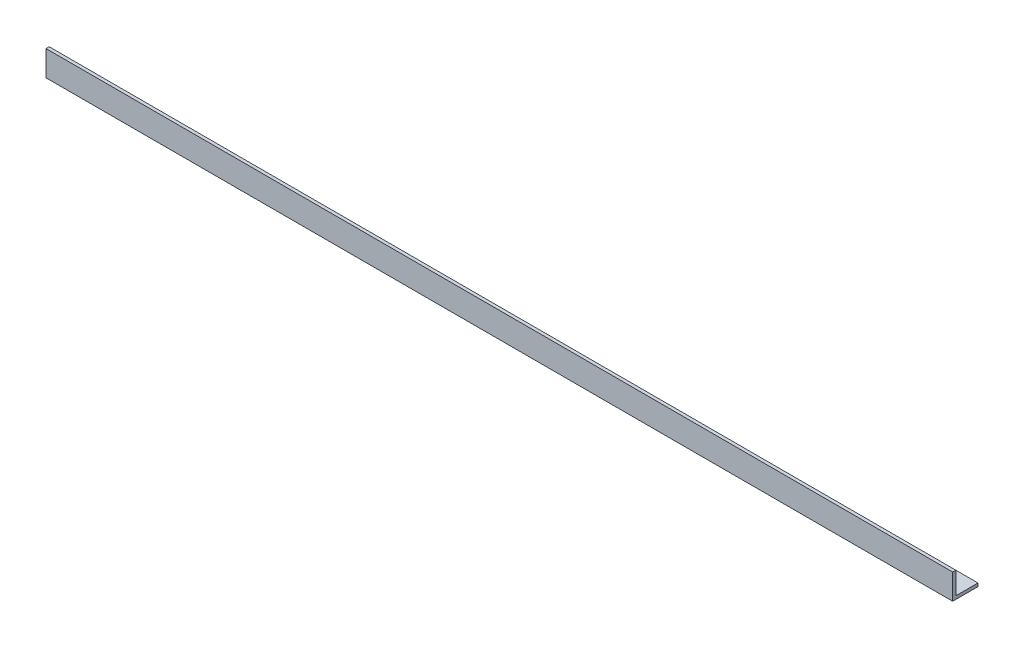
SolidWorks part; units mm, degrees
ref_plane "Front Plane" through (0, 0, 0) normal (0, 0, 1) x (1, 0, 0)
ref_plane "Top Plane" through (0, 0, 0) normal (0, 1, 0) x (1, 0, 0)
ref_plane "Right Plane" through (0, 0, 0) normal (1, 0, 0) x (0, 0, -1)
sketch "Sketch1" plane through (0, 0, 0) normal (1, 0, 0) x (0, 0, -1)
  line L0 (0, 0) -> (0, 25.4)
  line L1 (0, 25.4) -> (3.175, 25.4)
  line L2 (3.175, 25.4) -> (3.175, 3.175)
  line L3 (3.175, 3.175) -> (25.4, 3.175)
  line L4 (25.4, 3.175) -> (25.4, 0)
  line L5 (25.4, 0) -> (0, 0)
  dimension "D1" = 25.4
  dimension "D2" = 3.175
extrude "Boss-Extrude1" add sketch "Sketch1" along normal mid plane 908.05
